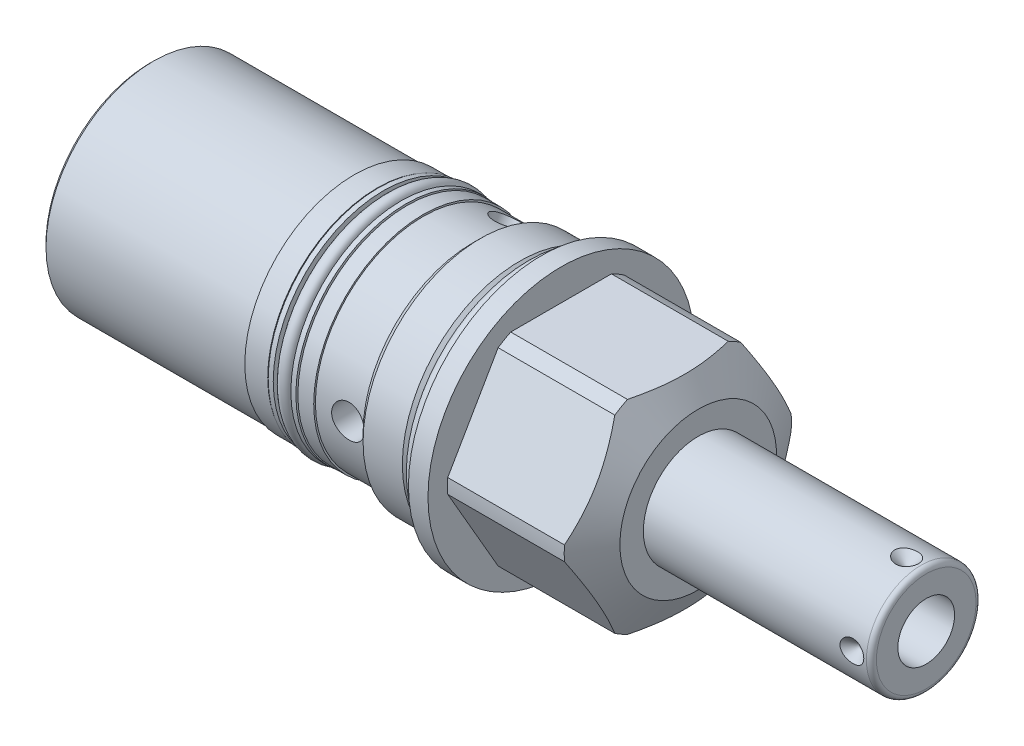
SolidWorks part; units mm, degrees
material "Alloy Steel"
ref_plane "Front Plane" through (0, 0, 0) normal (0, 0, 1) x (1, 0, 0)
ref_plane "Top Plane" through (0, 0, 0) normal (0, 1, 0) x (1, 0, 0)
ref_plane "Right Plane" through (0, 0, 0) normal (1, 0, 0) x (0, 0, -1)
ref_plane "Plane1" through (0, 0, 0) normal (1, 0, 0) x (0, 0, -1)
sketch "Sketch1" plane through (0, 0, 0) normal (1, 0, 0) x (0, 0, -1)
  circle A0 centre (0, 0) radius 26.9875
  dimension "D1" = 53.975
extrude "Extrude1" add sketch "Sketch1" along normal blind 31.75 and the other way blind 79.375
ref_plane "Plane2" through (0, 0, 0) normal (1, 0, 0) x (0, 0, -1)
sketch "Sketch2" plane through (0, 0, 0) normal (1, 0, 0) x (0, 0, -1)
  circle A0 centre (0, 0) radius 23.8125
  circle A1 centre (0, 0) radius 26.9875 construction
  circle A2 centre (0, 0) radius 26.9875
  dimension "D1" = 47.625
extrude "Cut-Extrude1" cut sketch "Sketch2" against normal up to next
ref_plane "Plane3" through (0, 0, 0) normal (0, 0, 1) x (1, 0, 0)
sketch "Sketch3" plane through (0, 0, 0) normal (0, 0, 1) x (1, 0, 0)
  line L0 (25.3342, 26.9875) -> (31.75, 15.875)
  line L1 (-8.1458, 0) -> (17.0188, 0) construction
  line L2 (31.75, 15.875) -> (31.75, 26.9875)
  line L3 (31.75, 26.9875) -> (25.3342, 26.9875)
  line L4 (31.75, 26.9875) -> (0, 26.9875) construction
  dimension "D1" = 31.75
  dimension "D2" = 30
revolve "Cut-Revolve1" cut sketch "Sketch3" angle 360 about L1
ref_plane "Plane5" through (3.175, 0, 0) normal (-1, 0, 0) x (0, 0, 1)
sketch "Sketch5" plane through (3.175, 0, 0) normal (-1, 0, 0) x (0, 0, 1)
  line L0 (-11.9151, 20.6375) -> (11.9151, 20.6375)
  line L1 (11.9151, 20.6375) -> (23.8301, 0)
  line L2 (23.8301, 0) -> (11.9151, -20.6375)
  line L3 (11.9151, -20.6375) -> (-11.9151, -20.6375)
  line L4 (-11.9151, -20.6375) -> (-23.8301, 0)
  line L5 (-23.8301, 0) -> (-11.9151, 20.6375)
  line L6 (0, 0) -> (18.7904, 0) construction
  line L7 (0, 0) -> (11.9151, 20.6375) construction
  line L8 (0, 0) -> (-11.9151, 20.6375) construction
  circle A0 centre (0, 0) radius 26.9875 construction
  circle A1 centre (0, 0) radius 26.9875
  dimension "D1" = 41.275
  dimension "D2" = 120
  dimension "D3" = 60
extrude "Cut-Extrude3" cut sketch "Sketch5" against normal up to next from offset 0.7874 offset against normal yes
ref_plane "Plane7" through (3.175, 0, 0) normal (-1, 0, 0) x (0, 0, 1)
sketch "Sketch7" plane through (3.9624, 0, 0) normal (-1, 0, 0) x (0, 0, 1)
  circle A0 centre (0, 0) radius 23.0251
  circle A1 centre (0, 0) radius 26.9875 construction
  circle A2 centre (0, 0) radius 26.9875
  dimension "D1" = 46.0502
extrude "Cut-Extrude5" cut sketch "Sketch7" against normal up to next
ref_plane "Plane9" through (0, 0, 0) normal (0, 0, 1) x (1, 0, 0)
sketch "Sketch9" plane through (0, 0, 0) normal (0, 0, 1) x (1, 0, 0)
  line L0 (0, 23.8125) -> (0, 22.3012)
  line L1 (0, 22.3012) -> (-2.8956, 22.3012)
  line L2 (-2.8956, 22.3012) -> (-4.4069, 23.8125)
  line L3 (-4.4206, 0) -> (0.2105, 0) construction
  line L4 (0, 23.8125) -> (-4.4069, 23.8125)
  line L5 (0, 23.8125) -> (-79.375, 23.8125) construction
  line L6 (0, 26.9875) -> (0, -26.9875) construction
  dimension "D1" = 2.8956
  dimension "D2" = 45
  dimension "D3" = 44.6024
revolve "Cut-Revolve3" cut sketch "Sketch9" angle 360 about L3
ref_plane "Plane10" through (0, 0, 0) normal (0, 0, 1) x (1, 0, 0)
sketch "Sketch10" plane through (0, 0, 0) normal (0, 0, 1) x (1, 0, 0)
  line L0 (-12.3698, 23.8125) -> (-13.9954, 22.1869)
  line L1 (-13.9954, 22.1869) -> (-79.375, 22.1869)
  line L2 (-55.947, 0) -> (-8.6516, 0) construction
  line L4 (-79.375, 23.8125) -> (-79.375, 22.1869)
  line L5 (-4.4069, 23.8125) -> (-4.4069, -23.8125) construction
  line L6 (-4.4069, 23.8125) -> (-79.375, 23.8125) construction
  line L7 (-12.3698, 23.8125) -> (-79.375, 23.8125)
  dimension "D1" = 44.3738
  dimension "D2" = 45
  dimension "D3" = 7.9629
revolve "Cut-Revolve4" cut sketch "Sketch10" angle 360 about L2
ref_plane "Plane12" through (0, 0, 0) normal (0, 0, 1) x (1, 0, 0)
sketch "Sketch12" plane through (0, 0, 0) normal (0, 0, 1) x (1, 0, 0)
  line L0 (-33.3248, 22.1869) -> (-33.3248, 20.1549)
  line L1 (-33.3248, 20.1549) -> (-27.2161, 20.1549)
  line L2 (-27.2161, 20.1549) -> (-27.2161, 22.1869)
  line L3 (-31.7506, 0) -> (-25.0311, 0) construction
  line L4 (-33.3248, 22.1869) -> (-27.2161, 22.1869)
  line L5 (-13.9954, 22.1869) -> (-79.375, 22.1869) construction
  line L6 (-79.375, 22.1869) -> (-79.375, -22.1869) construction
  dimension "D1" = 6.1087
  dimension "D2" = 40.3098
  dimension "D3" = 46.0502
revolve "Cut-Revolve6" cut sketch "Sketch12" angle 360 about L3
ref_plane "Plane14" through (0, 0, 0) normal (0, 0, 1) x (0, -1, 0)
sketch "Sketch14" plane through (0, 0, 0) normal (0, 0, 1) x (0, -1, 0)
  line L0 (22.1869, -79.375) -> (21.844, -79.375)
  line L1 (21.844, -79.375) -> (21.844, -37.973)
  line L2 (21.844, -37.973) -> (22.1869, -37.973)
  line L3 (22.1869, -37.973) -> (22.1869, -79.375)
  line L4 (22.1869, -13.9954) -> (21.844, -13.9954)
  line L5 (21.844, -13.9954) -> (21.844, -24.003)
  line L6 (21.844, -24.003) -> (22.1869, -24.003)
  line L7 (22.1869, -24.003) -> (22.1869, -13.9954)
  line L8 (0, -55.866) -> (0, -10.3518) construction
  line L9 (22.1869, -79.375) -> (22.1869, -33.3248) construction
  line L10 (22.1869, -27.2161) -> (22.1869, -13.9954) construction
  line L11 (-22.1869, -79.375) -> (22.1869, -79.375) construction
  dimension "D1" = 13.97
  dimension "D2" = 43.688
  dimension "D3" = 41.402
  dimension "D4" = 10.0076
revolve "Cut-Revolve8" cut sketch "Sketch14" angle 360 about L8
ref_plane "Plane15" through (0, 0, 0) normal (0, 0, 1) x (0, -1, 0)
sketch "Sketch15" plane through (0, 0, 0) normal (0, 0, 1) x (0, -1, 0)
  line L0 (0, -3.0937) -> (0, 0.1473) construction
  line L1 (-26.9875, 0) -> (26.9875, 0) construction
  circle A0 centre (23.7998, -1.4986) radius 1.4986
  dimension "D1" = 2.9972
  dimension "D2" = 1.4986
  dimension "D3" = 47.5996
revolve "Revolve1" add sketch "Sketch15" angle 360 about L0
ref_plane "Plane16" through (0, 0, 0) normal (0, 0, 1) x (0, -1, 0)
sketch "Sketch16" plane through (0, 0, 0) normal (0, 0, 1) x (0, -1, 0)
  line L0 (20.1549, -27.4701) -> (22.3393, -27.4701)
  line L1 (22.3393, -27.4701) -> (22.3393, -28.4861)
  line L2 (22.3393, -28.4861) -> (20.1549, -28.4861)
  line L3 (20.1549, -28.4861) -> (20.1549, -27.4701)
  line L4 (20.1549, -33.0708) -> (22.3393, -33.0708)
  line L5 (22.3393, -33.0708) -> (22.3393, -32.0548)
  line L6 (22.3393, -32.0548) -> (20.1549, -32.0548)
  line L7 (20.1549, -32.0548) -> (20.1549, -33.0708)
  line L8 (0, -31.4712) -> (0, -25.3105) construction
  line L9 (-22.1869, -27.2161) -> (22.1869, -27.2161) construction
  line L10 (22.1869, -33.3248) -> (-22.1869, -33.3248) construction
  line L11 (20.1549, -33.3248) -> (20.1549, -27.2161) construction
  dimension "D1" = 1.016
  dimension "D3" = 44.6786
  dimension "D4" = 0.254
  dimension "D5" = 0.254
revolve "Revolve2" add sketch "Sketch16" angle 360 about L8
ref_plane "Plane17" through (0, 0, 0) normal (0, 0, 1) x (0, -1, 0)
sketch "Sketch17" plane through (0, 0, 0) normal (0, 0, 1) x (0, -1, 0)
  line L0 (0, -31.7506) -> (0, -25.0311) construction
  line L1 (22.3393, -32.0548) -> (-22.3393, -32.0548) construction
  circle A0 centre (21.463, -30.2704) radius 1.3081
  point P0 (9.8298, -25.3365)
  point P1 (9.8298, -31.4452)
  dimension "D1" = 2.6162
  dimension "D2" = 42.926
  dimension "D3" = 1.7843
revolve "Revolve3" add sketch "Sketch17" angle 360 about L0
ref_plane "Plane18" through (0, 0, 0) normal (0, 0, 1) x (0, -1, 0)
sketch "S2D0001" plane through (0, 0, 0) normal (0, 0, 1) x (0, -1, 0)
  line L0 (0, 31.75) -> (-11.1125, 31.75)
  line L1 (-11.1125, 31.75) -> (-11.1125, 76.962)
  line L2 (-10.0965, 77.978) -> (0, 77.978)
  line L3 (0, 77.978) -> (0, 31.75)
  line L4 (0, 7.2658) -> (0, 37.3443) construction
  line L5 (15.875, 31.75) -> (-15.875, 31.75) construction
  line L6 (-26.9875, 0) -> (26.9875, 0) construction
  arc A0 (-10.0965, 77.978) -> (-11.1125, 76.962) centre (-10.0965, 76.962) ccw
  dimension "D2" = 1.016
  dimension "D1" = 22.225
  dimension "D3" = 77.978
revolve "Revolve4" add sketch "S2D0001" angle 360 about L4
ref_plane "Plane19" through (36.322, -2.8067, 0) normal (0, 0, 1) x (0, -1, 0)
sketch "Sketch19" plane through (36.322, -2.8067, 0) normal (0, 0, 1) x (0, -1, 0)
  line L0 (2.9464, 41.656) -> (2.9464, 24.638)
  line L1 (2.9464, 24.638) -> (-2.8067, 21.1812)
  line L2 (2.9464, 41.656) -> (-2.8067, 41.656)
  line L3 (-2.8067, 41.656) -> (-2.8067, 21.1812)
  line L4 (-2.8067, -18.6227) -> (-2.8067, 0.5923) construction
  line L5 (7.2898, 41.656) -> (-12.9032, 41.656) construction
  dimension "D1" = 11.5062
  dimension "D2" = 17.018
  dimension "D3" = 59
revolve "Cut-Revolve9" cut sketch "Sketch19" angle 360 about L4
ref_plane "Plane20" through (32.3596, 0, -5.5562) normal (0, 1, 0) x (1, 0, 0)
sketch "S2D0002" plane through (32.3596, 0, -5.5562) normal (0, 1, 0) x (1, 0, 0)
  line L0 (41.656, 5.5563) -> (44.069, 5.5563)
  line L1 (44.069, 5.5563) -> (41.656, 3.1433)
  line L2 (41.656, 5.5563) -> (41.656, 3.1433)
  line L3 (41.656, -3.3652) -> (41.656, 0.0794) construction
  line L4 (44.6024, 5.5562) -> (-0.6096, 5.5562) construction
  line L5 (45.6184, -15.6527) -> (45.6184, 4.5402) construction
  dimension "D1" = 3.9624
  dimension "D2" = 45
  dimension "D3" = 4.826
revolve "Cut-Revolve10" cut sketch "S2D0002" angle 360 about L3
pattern_circular "CirPattern1" count 4 over 360 about axis through (7.2658, 0, 0) along (-1, 0, 0) of "Cut-Revolve10"
chamfer "Chamfer1" distance 0.762 angle 45 1 edges at (-79.375, 0, 21.844)
sketch "Sketch23" plane through (0, 0, 0) normal (0, 0, 1) x (1, 0, 0)
  line L0 (-79.375, 21.082) -> (-79.375, -21.082) construction
  circle A0 centre (-17.399, 0) radius 3.3147
  dimension "D1" = 6.6294
  dimension "D2" = 61.976
extrude "Cut-Extrude7" cut sketch "Sketch23" along normal through all
sketch "Sketch24" plane through (0, 0, 0) normal (0, 0, 1) x (1, 0, 0)
  line L0 (0, 0) -> (-56.0091, 0) construction
  line L1 (-79.375, 6.1849) -> (-76.8223, 5.6423)
  line L2 (-79.375, 21.082) -> (-79.375, -21.082) construction
  line L3 (-76.8223, 5.6423) -> (-76.1584, 4.9784)
  line L4 (-76.1584, 4.9784) -> (-65.1002, 4.9784)
  line L5 (-65.1002, 4.9784) -> (-65.1002, 0)
  line L6 (-65.1002, 0) -> (-79.375, 0)
  line L7 (-79.375, 0) -> (-79.375, 6.1849)
  dimension "D1" = 9.9568
  dimension "D2" = 14.2748
  dimension "D3" = 45
  dimension "D4" = 12
  dimension "D5" = 12.3698
  dimension "D6" = 2.5527
revolve "Cut-Revolve11" cut sketch "Sketch24" angle 360 about L0
sketch "Sketch26" plane through (-79.375, 0, 0) normal (-1, 0, 0) x (0, 0, 1)
  circle A0 centre (0, 0) radius 17.7927
extrude "Extrude2" add sketch "Sketch26" along normal blind 0.508
sketch "Sketch27" plane through (-79.883, 0, 0) normal (-1, 0, 0) x (0, 0, 1)
  circle A0 centre (0, 0) radius 6.1849
extrude "Cut-Extrude8" cut sketch "Sketch27" against normal blind 0.508
pattern_circular "CirPattern2" count 3 over 360 about axis through (7.2658, 0, 0) along (-1, 0, 0) of "Cut-Extrude7"
